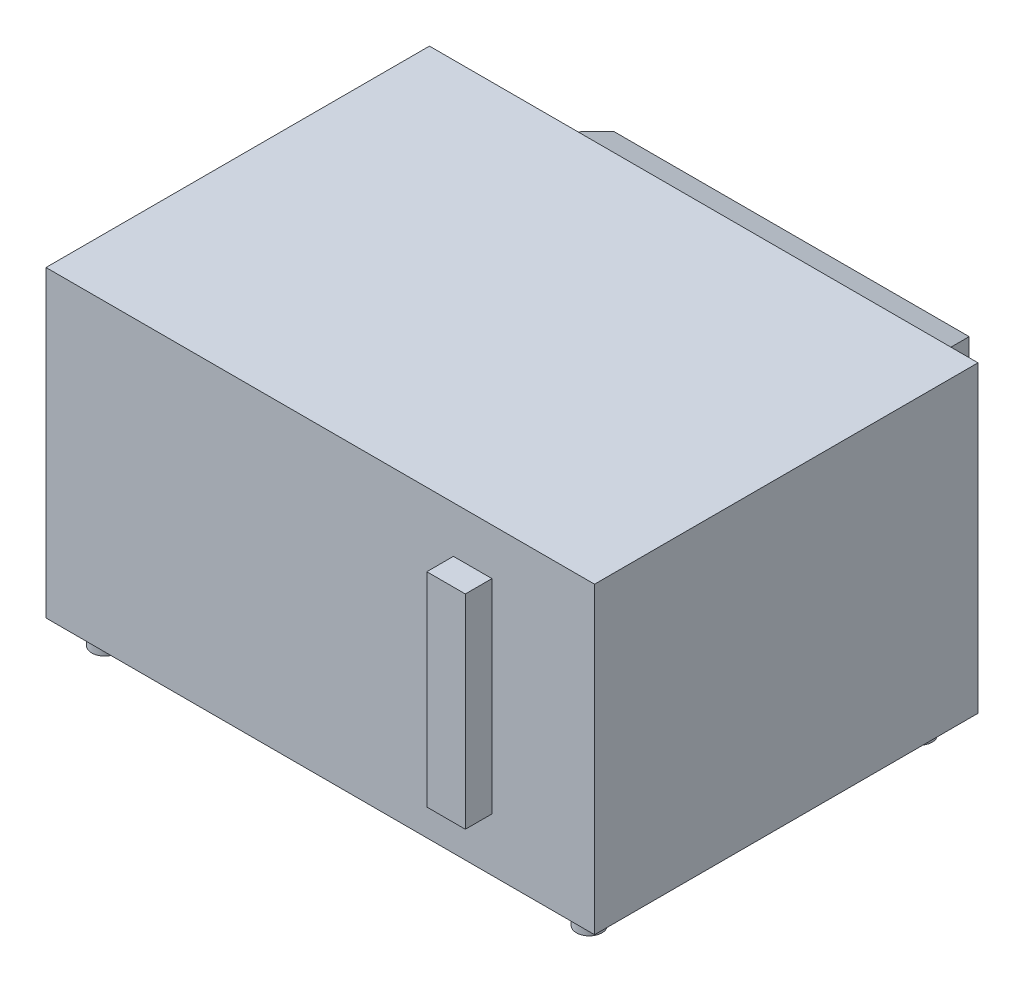
SolidWorks part; units mm, degrees
ref_plane "Спереди" through (0, 0, 0) normal (0, 0, 1) x (1, 0, 0)
ref_plane "Сверху" through (0, 0, 0) normal (0, 1, 0) x (1, 0, 0)
ref_plane "Справа" through (0, 0, 0) normal (1, 0, 0) x (0, 0, -1)
sketch "Эскиз2" plane through (0, 0, 0) normal (0, 1, 0) x (1, 0, 0)
  line L1 (0, 0) -> (515, 0)
  line L2 (0, 0) -> (0, 360)
  line L3 (0, 360) -> (515, 360)
  line L4 (515, 0) -> (515, 360)
extrude "Бобышка-Вытянуть1" add sketch "Эскиз2" along normal blind 285
sketch "Эскиз3" plane through (0, 0, 0) normal (0, -1, 0) x (1, 0, 0)
  line L0 (0, -180) -> (357.8146, -180) construction
  line L1 (0, -360) -> (0, 0) construction
  line L2 (257.5, 0) -> (257.5, -255.9154) construction
  line L3 (0, 0) -> (515, 0) construction
  circle A0 centre (30, -25) radius 12
  circle A1 centre (30, -335) radius 12
  circle A2 centre (485, -335) radius 12
  circle A3 centre (485, -25) radius 12
extrude "Бобышка-Вытянуть2" add sketch "Эскиз3" along normal blind 20
sketch "Эскиз4" plane through (0, 0, 0) normal (0, 0, 1) x (1, 0, 0)
  line L1 (382.5126, 241.3978) -> (418.6878, 241.3978)
  line L2 (382.5126, 241.3978) -> (382.5126, 50.0707)
  line L3 (382.5126, 50.0707) -> (418.6878, 50.0707)
  line L4 (418.6878, 241.3978) -> (418.6878, 50.0707)
extrude "Бобышка-Вытянуть3" add sketch "Эскиз4" along normal blind 25
sketch "Эскиз5" plane through (0, 0, -360) normal (0, 0, -1) x (-1, 0, 0)
  line L1 (-449.3399, 56.097) -> (-60.3753, 56.097)
  line L2 (-449.3399, 56.097) -> (-449.3399, 244.766)
  line L3 (-449.3399, 244.766) -> (-60.3753, 244.766)
  line L4 (-60.3753, 56.097) -> (-60.3753, 244.766)
extrude "Бобышка-Вытянуть4" add sketch "Эскиз5" along normal blind 85 draft 18
